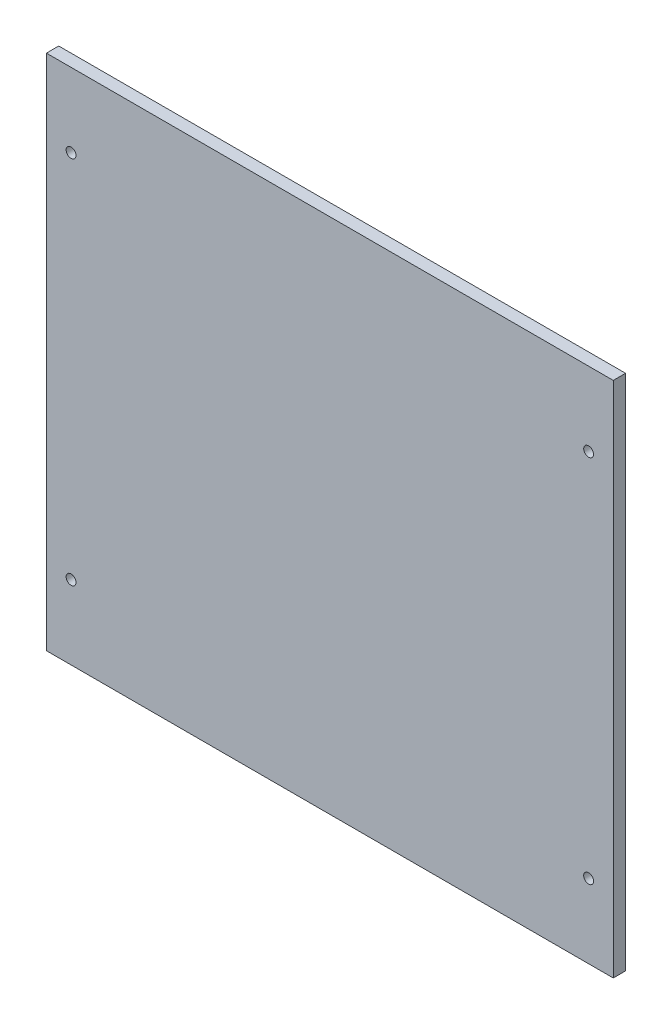
SolidWorks part; units mm, degrees
ref_plane "Front Plane" through (0, 0, 0) normal (0, 0, 1) x (1, 0, 0)
ref_plane "Top Plane" through (0, 0, 0) normal (0, 1, 0) x (1, 0, 0)
ref_plane "Right Plane" through (0, 0, 0) normal (1, 0, 0) x (0, 0, -1)
sketch "Sketch1" plane through (0, 0, 0) normal (0, 0, 1) x (1, 0, 0)
  line L1 (-115, 105) -> (115, 105)
  line L2 (-115, 105) -> (-115, -105)
  line L3 (-115, -105) -> (115, -105)
  line L4 (115, 105) -> (115, -105)
  line L5 (-115, 105) -> (115, -105) construction
  line L6 (-115, -105) -> (115, 105) construction
  point P0 (0, 0)
  dimension "D1" = 230
  dimension "D2" = 210
extrude "Boss-Extrude1" add sketch "Sketch1" along normal blind 5
sketch "Sketch2" plane through (0, 0, 5) normal (0, 0, 1) x (1, 0, 0)
  line L0 (-115, 105) -> (-115, -105) construction
  line L1 (115, 105) -> (-115, 105) construction
  line L2 (-115, -105) -> (115, -105) construction
  line L3 (0, 105) -> (0, -105) construction
  circle A0 centre (-105, 75) radius 2
  circle A1 centre (-105, -75) radius 2
  circle A2 centre (105, -75) radius 2
  circle A3 centre (105, 75) radius 2
  dimension "D1" = 4
  dimension "D2" = 4
  dimension "D3" = 10
  dimension "D4" = 10
  dimension "D5" = 30
  dimension "D6" = 30
extrude "Cut-Extrude1" cut sketch "Sketch2" against normal blind 25
